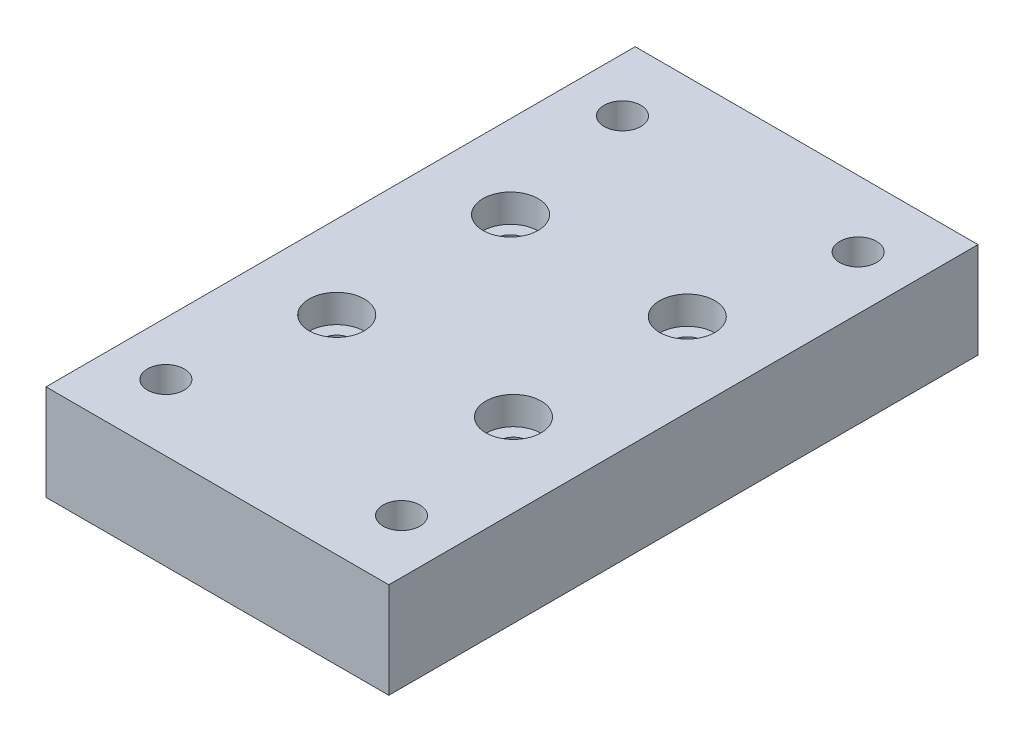
SolidWorks part; units mm, degrees
material "6061-T6 (SS)"
ref_plane "Front Plane" through (0, 0, 0) normal (0, 0, 1) x (1, 0, 0)
ref_plane "Top Plane" through (0, 0, 0) normal (0, 1, 0) x (1, 0, 0)
ref_plane "Right Plane" through (0, 0, 0) normal (1, 0, 0) x (0, 0, -1)
sketch "Sketch1" plane through (0, 0, 0) normal (0, 1, 0) x (1, 0, 0)
  line L1 (-29.5593, -50.8) -> (29.5593, -50.8)
  line L2 (-29.5593, -50.8) -> (-29.5593, 50.8)
  line L3 (-29.5593, 50.8) -> (29.5593, 50.8)
  line L4 (29.5593, -50.8) -> (29.5593, 50.8)
  line L5 (-29.5593, -50.8) -> (29.5593, 50.8) construction
  line L6 (-29.5593, 50.8) -> (29.5593, -50.8) construction
  point P0 (0, 0)
  dimension "D1" = 101.6
  dimension "D2" = 59.1185
extrude "Boss-Extrude1" add sketch "Sketch1" along normal blind 16.51
hole_wizard "CBORE for #10 Socket Head Cap Screw1" positions "Sketch2" profile "Sketch3" counterbore size "#10" standard "ANSI Inch"
sketch "Sketch2" plane through (-223.3968, 16.51, 0) normal (0, 1, 0) x (0, 0, 1)
  point P0 (-14.986, 208.1568)
  point P1 (14.986, 208.1568)
  point P2 (14.986, 238.6368)
  point P3 (-14.986, 238.6368)
sketch "Sketch3" plane through (-15.24, 16.51, -14.986) normal (1, 0, 0) x (0, 0, 1)
  line L0 (0, 0) -> (0, 15.24)
  line L1 (0, 15.24) -> (2.5527, 15.24)
  line L2 (2.5527, 15.24) -> (2.5527, 4.826)
  line L3 (2.5527, 4.826) -> (4.7625, 4.826)
  line L4 (4.7625, 4.826) -> (4.7625, 0)
  line L5 (4.7625, 0) -> (0, 0)
  line L6 (0, -6.35) -> (0, 107.95) construction
  dimension "Thru Hole Dia." = 5.1054
  dimension "Thru Hole Depth" = 15.24
  dimension "C'Bore Dia." = 9.525
  dimension "C'Bore Depth" = 4.826
hole_wizard "1/4 (0.25) Diameter Hole1" positions "Sketch4" profile "Sketch5" hole size "1/4" standard "ANSI Inch" end condition through all
sketch "Sketch4" plane through (0, 16.51, 0) normal (0, 1, 0) x (1, 0, 0)
  line L0 (20.32, 39.37) -> (20.32, -39.37) construction
  line L3 (29.5593, -50.8) -> (29.5593, 50.8) construction
  line L4 (20.32, 39.37) -> (-20.32, 39.37) construction
  line L6 (29.5593, 50.8) -> (-29.5593, 50.8) construction
  point P0 (20.32, -39.37)
  point P2 (-20.32, -39.37)
  point P4 (-20.32, 39.37)
  point P6 (20.32, 39.37)
  point P16 (20.32, 0)
  point P19 (29.5593, 0)
  point P25 (0, 39.37)
  point P28 (0, 50.8)
  dimension "D1" = 78.74
  dimension "D2" = 40.64
sketch "Sketch5" plane through (20.32, 16.51, 39.37) normal (1, 0, 0) x (0, 0, 1)
  line L0 (0, 0) -> (0, 16.51)
  line L1 (0, 16.51) -> (3.175, 16.51)
  line L2 (3.175, 16.51) -> (3.175, 0)
  line L5 (3.175, 0) -> (0, 0)
  line L11 (0, -6.35) -> (0, 107.95) construction
  dimension "Thru Hole Dia." = 6.35
  dimension "Thru Hole Depth" = 16.51
